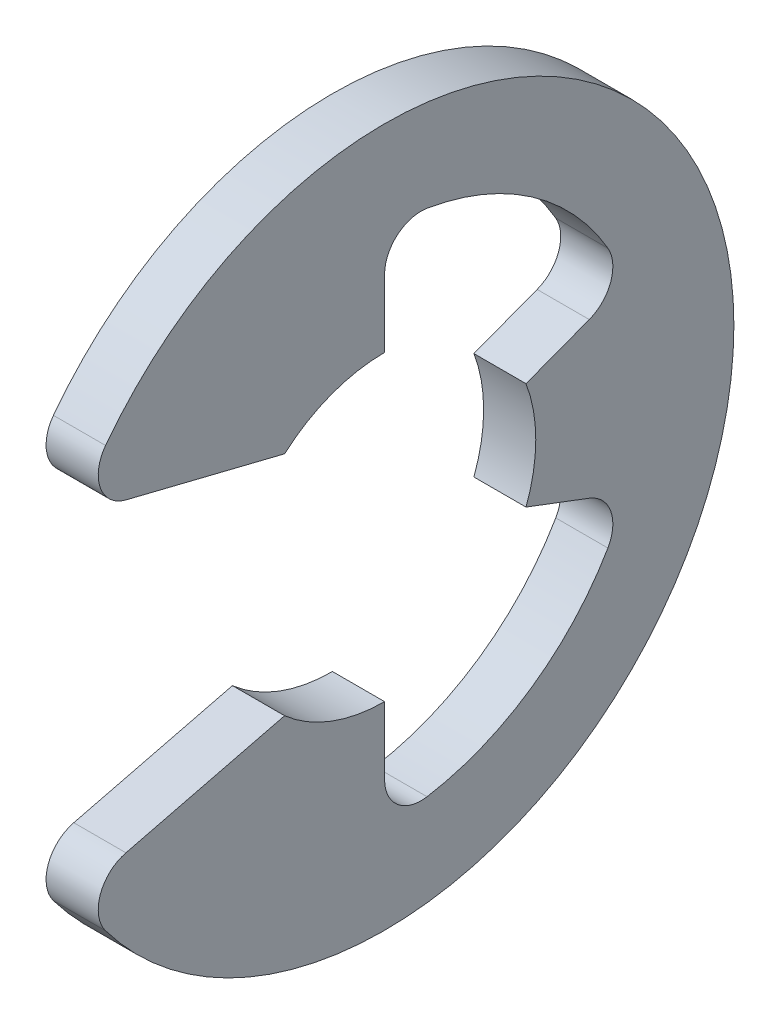
SolidWorks part; units mm, degrees
ref_plane "Front" through (0, 0, 0) normal (0, 0, 1) x (1, 0, 0)
ref_plane "Top" through (0, 0, 0) normal (0, 1, 0) x (1, 0, 0)
ref_plane "Right" through (0, 0, 0) normal (1, 0, 0) x (0, 0, -1)
sketch "Sketch1" plane through (0, 0, 0) normal (1, 0, 0) x (0, 0, -1)
  line L0 (-3.7499, -2.0097) -> (-1.218, -1.3811)
  line L1 (-3.7499, 2.0097) -> (-1.218, 1.3811)
  line L2 (0, -1.8415) -> (0, -3.1463)
  line L3 (0, 1.8415) -> (0, 3.1463)
  line L4 (1.7226, -0.6511) -> (2.9431, -1.1124)
  line L5 (1.7226, 0.6511) -> (2.9431, 1.1124)
  line L6 (0, 0) -> (-4.445, 0) construction
  line L7 (1.7226, 0.6511) -> (1.7226, -0.6511) construction
  line L8 (0, -1.8415) -> (-1.218, -1.3811) construction
  line L9 (0, 4.2545) -> (0, -4.2545) construction
  circle A1 centre (0, 0) radius 4.445 construction
  circle A2 centre (0, 0) radius 1.8415 construction
  arc A3 (-3.7499, -2.0097) -> (-3.7499, 2.0097) centre (0, 0) ccw
  arc A4 (-1.218, -1.3811) -> (0, -1.8415) centre (0, 0) ccw
  arc A5 (-1.218, 1.3811) -> (0, 1.8415) centre (0, 0) cw
  arc A6 (1.7226, 0.6511) -> (1.7226, -0.6511) centre (0, 0) cw
  arc A7 (0, -3.1463) -> (2.9431, -1.1124) centre (0, 0) ccw
  arc A8 (2.9431, 1.1124) -> (0, 3.1463) centre (0, 0) ccw
  dimension "D" = 3.683
  dimension "D1" = 3.1463
  dimension "OD" = 8.509
  dimension "D2" = 2.0939
  dimension "D3" = 2.7622
extrude "Extrude1" add sketch "Sketch1" along normal mid plane 0.635
fillet "Fillet1" radius 0.4445 6 edges at (0, -3.1463, 0) (0, 3.1463, 0) (0, -2.0097, 3.7499) (0, 2.0097, 3.7499) (0, -1.1124, -2.9431) (0, 1.1124, -2.9431)
sketch "Sketch3" plane through (0, 0, 0) normal (0, 1, 0) x (1, 0, 0)
  line L0 (0.3683, 2.3876) -> (0.3683, 1.8669)
  line L1 (0.3683, 1.8669) -> (-0.3683, 1.8669)
  line L2 (-0.3683, 1.8669) -> (-0.3683, 2.3876)
  line L3 (-0.3683, 2.3876) -> (-7.9185, 2.3876)
  line L4 (3.1306, 0) -> (3.1305, 2.1272)
  line L5 (-7.9185, 2.3876) -> (-7.9185, 0)
  line L6 (-7.9185, 0) -> (3.1306, 0)
  line L8 (3.1306, 0) -> (3.1305, 2.3876) construction
  line L9 (3.1305, 2.3876) -> (0.3683, 2.3876) construction
  line L10 (3.1306, 0) -> (17.2631, 0) construction
  line L11 (3.1305, 2.1272) -> (2.8702, 2.3876)
  line L12 (2.8702, 2.3876) -> (0.3683, 2.3876)
  point P2 (0, 1.8669)
  point P5 (0.3683, 2.1272)
  dimension "D2" = 11.049
  dimension "D1" = 2.7622
  dimension "D3" = 45
revolve "Revolve2" [suppressed] add sketch "Sketch3" angle 360 about L10
equation "\"D2@Sketch3\" = \"W@Sketch3\"*15"
equation "\"D1@Sketch3\" = \"D2@Sketch3\"/4"
equation "\"D1@Sketch1\" = (\"OD@Sketch1\"+\"D@Sketch1\")/3.875"
equation "\"D3@Sketch1\" = \"D@Sketch1\"*.75"
equation "\"D1@Fillet1\" = \"D1@Extrude1\"*.7"
